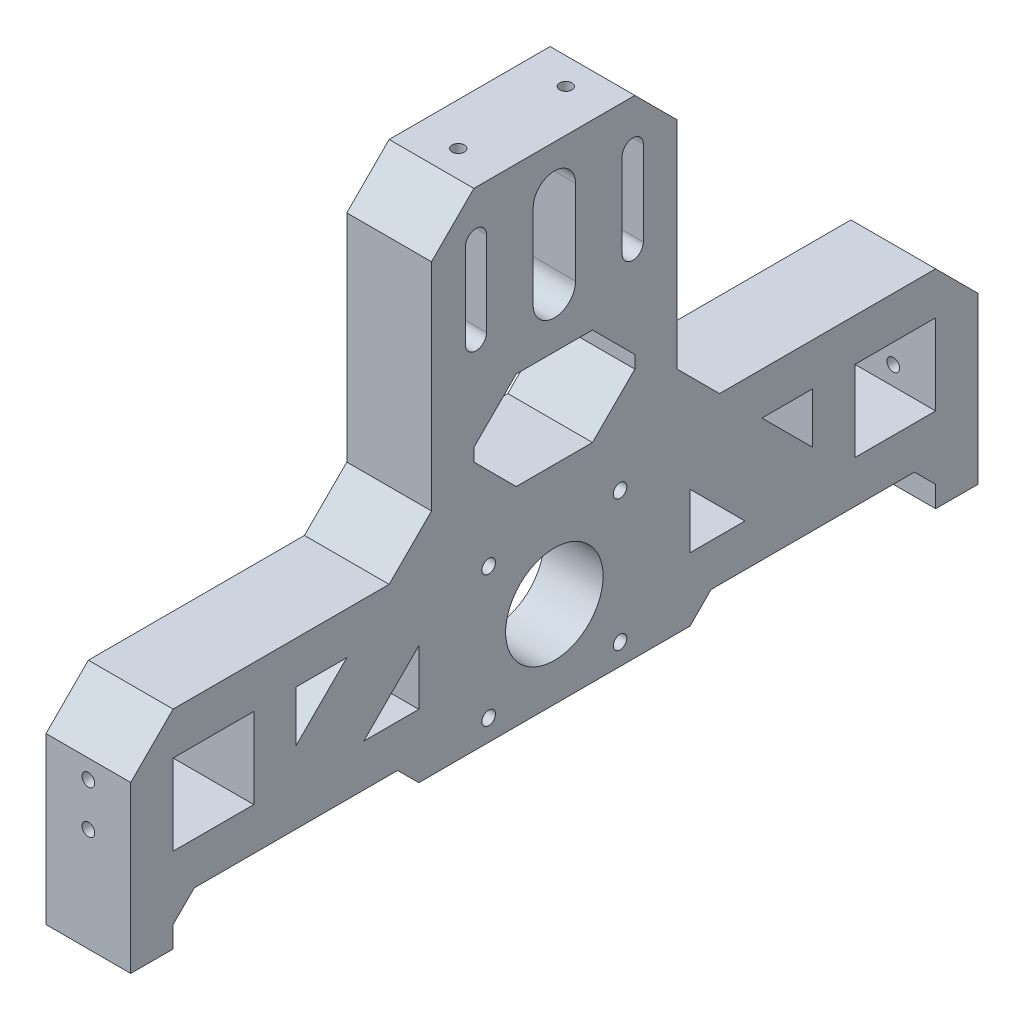
SolidWorks part; units mm, degrees
ref_plane "Front Plane" through (0, 0, 0) normal (0, 0, 1) x (1, 0, 0)
ref_plane "Top Plane" through (0, 0, 0) normal (0, 1, 0) x (1, 0, 0)
ref_plane "Right Plane" through (0, 0, 0) normal (1, 0, 0) x (0, 0, -1)
sketch "Sketch1" plane through (0, 0, 0) normal (1, 0, 0) x (0, 0, -1)
  line L1 (0, 0) -> (-100, 0)
  line L2 (0, 0) -> (0, 120)
  line L3 (0, 120) -> (-100, 120)
  line L4 (-100, 0) -> (-100, 120)
  dimension "D1" = 100
  dimension "D2" = 120
extrude "Boss-Extrude1" add sketch "Sketch1" along normal blind 20
sketch "Sketch2" plane through (20, 0, 0) normal (1, 0, 0) x (0, 0, -1)
  line L0 (-100, 0) -> (0, 0) construction
  line L1 (-90, 39.05) -> (-70.95, 39.05)
  line L2 (-90, 39.05) -> (-90, 20)
  line L3 (-90, 20) -> (-70.95, 20)
  line L4 (-70.95, 39.05) -> (-70.95, 20)
  line L5 (-100, 120) -> (-100, 0) construction
  dimension "D1" = 19.05
  dimension "D2" = 20
  dimension "D3" = 10
extrude "Cut-Extrude1" cut sketch "Sketch2" against normal blind 20
sketch "Sketch3" plane through (0, 0, 100) normal (0, 0, 1) x (1, 0, 0)
  line L0 (10, 34.605) -> (10, 24.445) construction
  line L1 (20, 39.05) -> (20, 20) construction
  line L2 (20, 0) -> (0, 0) construction
  circle A0 centre (10, 34.605) radius 1.5
  circle A1 centre (10, 24.445) radius 1.5
  point P6 (20, 29.525)
  point P7 (10, 29.525)
  point P10 (10, 0)
  dimension "D1" = 3
  dimension "D2" = 10.16
extrude "Cut-Extrude2" cut sketch "Sketch3" against normal blind 20
mirror "Mirror1" about plane through (20, 0, 0) normal (0, 0, 1) of "Cut-Extrude2", "Cut-Extrude1", "Boss-Extrude1"
sketch "Sketch5" plane through (20, 0, 0) normal (1, 0, 0) x (0, 0, -1)
  line L0 (0, 0) -> (0, 120) construction
  line L1 (-100, 0) -> (100, 0) construction
  line L2 (100, 120) -> (-100, 120) construction
  line L3 (-15.5, 10) -> (-15.5, 41) construction
  line L4 (-15.5, 10) -> (15.5, 10) construction
  line L5 (-15.5, 41) -> (15.5, 41) construction
  line L6 (15.5, 10) -> (15.5, 41) construction
  line L7 (-15.5, 10) -> (15.5, 41) construction
  line L8 (-15.5, 41) -> (15.5, 10) construction
  circle A0 centre (0, 25.5) radius 11.5
  circle A1 centre (-15.5, 41) radius 1.6
  circle A2 centre (15.5, 41) radius 1.6
  circle A3 centre (15.5, 10) radius 1.6
  circle A4 centre (-15.5, 10) radius 1.6
  dimension "D1" = 23
  dimension "D2" = 3.2
  dimension "D3" = 31
  dimension "D4" = 10
extrude "Cut-Extrude3" cut sketch "Sketch5" against normal blind 20
sketch "Sketch6" plane through (0, 0, 0) normal (-1, 0, 0) x (0, 0, 1)
  line L0 (22, 3.5) -> (-22, 3.5)
  line L1 (22, 3.5) -> (22, 47.5)
  line L2 (-22, 3.5) -> (-22, 47.5)
  line L3 (22, 47.5) -> (-22, 47.5)
  line L4 (22, 3.5) -> (-22, 47.5) construction
  line L5 (-22, 3.5) -> (22, 47.5) construction
  circle A0 centre (0, 25.5) radius 11.5 construction
  point P1 (0, 25.5)
  dimension "D1" = 44
  dimension "D2" = 44
extrude "Motor indent" cut sketch "Sketch6" against normal blind 6
sketch "Sketch7" plane through (0, 0, 0) normal (-1, 0, 0) x (0, 0, 1)
  line L1 (0, 109.05) -> (0, 89.05) construction
  line L2 (5, 109.05) -> (5, 89.05)
  line L3 (-5, 109.05) -> (-5, 89.05)
  line L4 (-70.95, 39.05) -> (-90, 39.05) construction
  line L5 (-18.5, 109.05) -> (-18.5, 89.05) construction
  line L6 (-16, 109.05) -> (-16, 89.05)
  line L7 (-21, 109.05) -> (-21, 89.05)
  line L8 (0, 120) -> (0, 47.5) construction
  line L9 (-100, 120) -> (100, 120) construction
  line L10 (22, 47.5) -> (-22, 47.5) construction
  line L11 (18.5, 109.05) -> (18.5, 89.05) construction
  line L12 (16, 109.05) -> (16, 89.05)
  line L13 (21, 109.05) -> (21, 89.05)
  arc A1 (5, 109.05) -> (-5, 109.05) centre (0, 109.05) ccw
  arc A2 (-5, 89.05) -> (5, 89.05) centre (0, 89.05) ccw
  arc A3 (-16, 109.05) -> (-21, 109.05) centre (-18.5, 109.05) ccw
  arc A4 (-21, 89.05) -> (-16, 89.05) centre (-18.5, 89.05) ccw
  arc A5 (16, 109.05) -> (21, 109.05) centre (18.5, 109.05) cw
  arc A6 (21, 89.05) -> (16, 89.05) centre (18.5, 89.05) cw
  point P2 (0, 99.05)
  point P9 (-18.5, 99.05)
  point P20 (18.5, 99.05)
  dimension "D1" = 10
  dimension "D2" = 20
  dimension "D3" = 60
  dimension "D4" = 5
  dimension "D5" = 18.5
extrude "Bearing Block" cut sketch "Sketch7" against normal through all
sketch "Sketch8" plane through (20, 0, 0) normal (1, 0, 0) x (0, 0, -1)
  line L0 (-29, 120) -> (-29, 49.05)
  line L1 (100, 120) -> (-100, 120) construction
  line L2 (-29, 49.05) -> (-100, 49.05)
  line L3 (-100, 120) -> (-100, 0) construction
  line L4 (-70.95, 39.05) -> (-90, 39.05) construction
  line L5 (-21, 89.05) -> (-21, 109.05) construction
  line L6 (-100, 49.05) -> (-100, 120)
  line L7 (-100, 120) -> (-29, 120)
  line L8 (0, 55) -> (0, -55) construction
  line L9 (100, 120) -> (29, 120)
  line L10 (100, 49.05) -> (100, 120)
  line L11 (29, 49.05) -> (100, 49.05)
  line L12 (29, 120) -> (29, 49.05)
  dimension "D1" = 10
  dimension "D2" = 8
extrude "Cut-Extrude6" cut sketch "Sketch8" against normal through all
chamfer "Chamfer1" distance 10 angle 45 6 edges at (10, 49.05, 100) (10, 49.05, 29) (10, 120, 29) (10, 120, -29) (10, 49.05, -29) (10, 49.05, -100)
sketch "Sketch10" plane through (0, 0, 0) normal (-1, 0, 0) x (0, 0, 1)
  line L0 (100, 0) -> (-100, 0) construction
  line L1 (-90, 0) -> (-32, 0)
  line L2 (-90, 0) -> (-90, 10)
  line L3 (-90, 10) -> (-32, 10)
  line L4 (-32, 0) -> (-32, 10)
  line L5 (-90, 20) -> (-70.95, 20) construction
  line L6 (-100, 39.05) -> (-100, 0) construction
  line L7 (-22, 47.5) -> (-22, 3.5) construction
  line L8 (0, -55) -> (0, 55) construction
  line L9 (32, 0) -> (32, 10)
  line L10 (90, 10) -> (32, 10)
  line L11 (90, 0) -> (90, 10)
  line L12 (90, 0) -> (32, 0)
  dimension "D1" = 10
  dimension "D2" = 10
  dimension "D3" = 10
extrude "Cut-Extrude7" cut sketch "Sketch10" against normal through all
chamfer "Chamfer2" distance 5 angle 45 4 edges at (10, 10, -90) (10, 10, -32) (10, 10, 32) (10, 10, 90)
chamfer "Chamfer3" distance 4.5 angle 45 4 edges at (3, 3.5, 22) (3, 3.5, -22) (3, 47.5, 22) (3, 47.5, -22)
sketch "Sketch11" plane through (0, 120, 0) normal (0, 1, 0) x (1, 0, 0)
  line L0 (10, -12.7) -> (10, 12.7) construction
  line L1 (0, 0) -> (10, 0) construction
  line L2 (0, 19) -> (0, -19) construction
  line L3 (10, 0) -> (20, 0) construction
  line L4 (20, 19) -> (20, -19) construction
  circle A0 centre (10, -12.7) radius 1.45
  circle A1 centre (10, 12.7) radius 1.45
  dimension "D1" = 25.4
  dimension "D2" = 2.9
extrude "Cut-Extrude8" cut sketch "Sketch11" against normal blind 10
sketch "Sketch12" plane through (20, 0, 0) normal (1, 0, 0) x (0, 0, -1)
  line L0 (-29, 59.05) -> (-29, 110) construction
  line L1 (-19, 77.05) -> (19, 77.05)
  line L2 (-19, 77.05) -> (-19, 54.05)
  line L3 (-19, 54.05) -> (19, 54.05)
  line L4 (19, 77.05) -> (19, 54.05)
  line L5 (29, 110) -> (29, 59.05) construction
  line L6 (39, 49.05) -> (29, 59.05) construction
  arc A0 (-5, 89.05) -> (5, 89.05) centre (0, 89.05) ccw construction
  point P13 (34, 54.05)
  dimension "D1" = 10
  dimension "D2" = 10
  dimension "D3" = 12
  dimension "D4" = 0
extrude "Cut-Extrude9" cut sketch "Sketch12" against normal through all
chamfer "Chamfer4" distance 10 angle 45 4 edges at (10, 54.05, -19) (10, 77.05, -19) (10, 77.05, 19) (10, 54.05, 19)
sketch "Sketch13" plane through (0, 0, 0) normal (-1, 0, 0) x (0, 0, 1)
  line L0 (-49, 39.05) -> (-60.95, 27.1)
  line L1 (-60.95, 27.1) -> (-60.95, 39.05)
  line L2 (-60.95, 39.05) -> (-49, 39.05)
  line L3 (-29, 59.05) -> (-39, 49.05) construction
  line L4 (-39, 49.05) -> (-90, 49.05) construction
  line L5 (-70.95, 20) -> (-70.95, 39.05) construction
  line L6 (-32, 33) -> (-45, 20)
  line L7 (-45, 20) -> (-32, 20)
  line L8 (-32, 20) -> (-32, 33)
  line L9 (-32, 26.5) -> (-22, 26.5) construction
  line L10 (-22, 43) -> (-22, 8) construction
  line L11 (-41.4683, 10) -> (-41.4683, 20) construction
  line L12 (-37, 10) -> (-85, 10) construction
  line L13 (-22, 43) -> (-17.5, 47.5) construction
  line L14 (-54.9515, 39.05) -> (-54.9515, 49.05) construction
  dimension "D1" = 10
  dimension "D2" = 10
extrude "Cut-Extrude10" cut sketch "Sketch13" against normal through all
mirror "Mirror2" about plane through (0, 0, 0) normal (0, 0, 1) of "Cut-Extrude10"
sketch "Sketch14" plane through (20, 0, 0) normal (1, 0, 0) x (0, 0, -1)
  line L1 (-32, 0) -> (32, 0)
  line L2 (-32, 0) -> (-32, 5)
  line L3 (-32, 5) -> (32, 5)
  line L4 (32, 0) -> (32, 5)
extrude "Cut-Extrude11" cut sketch "Sketch14" against normal through all
